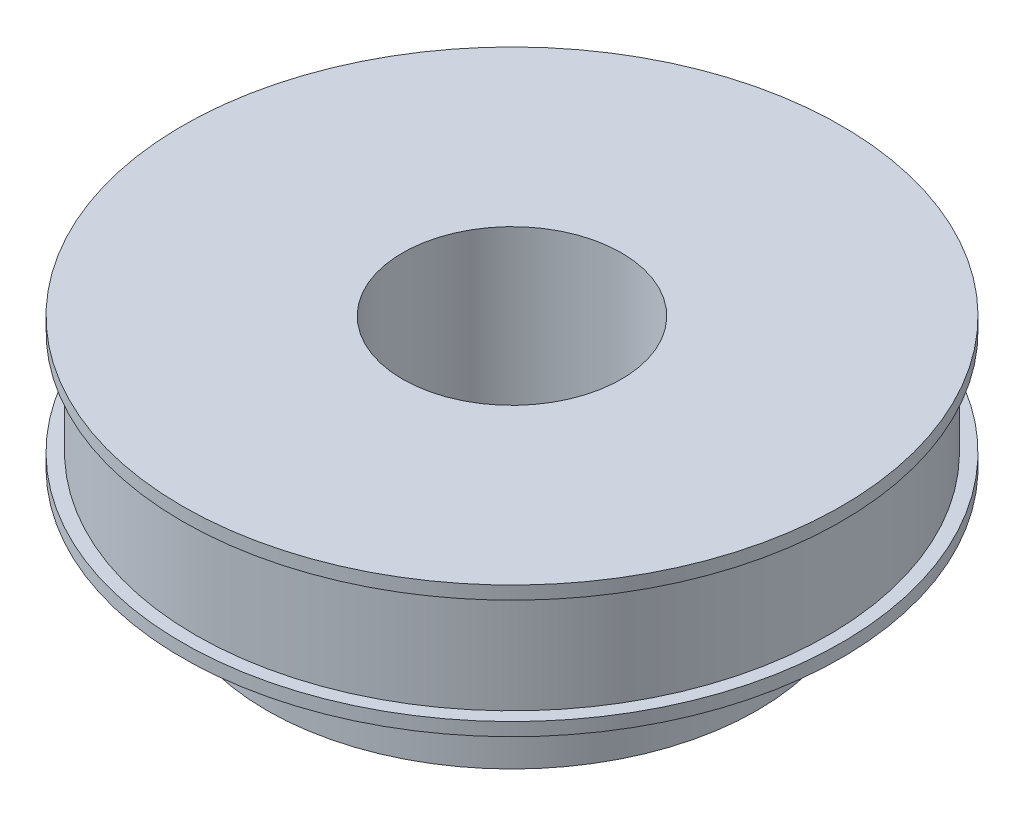
SolidWorks part; units mm, degrees
material "4032-T6"
ref_plane "Front Plane" through (0, 0, 0) normal (0, 0, 1) x (1, 0, 0)
ref_plane "Top Plane" through (0, 0, 0) normal (0, 1, 0) x (1, 0, 0)
ref_plane "Right Plane" through (0, 0, 0) normal (1, 0, 0) x (0, 0, -1)
sketch "Sketch1" plane through (0, 0, 0) normal (0, 1, 0) x (1, 0, 0)
  circle A0 centre (0, 0) radius 36.125
  dimension "D1" = 72.25
extrude "Boss-Extrude1" add sketch "Sketch1" along normal blind 12
sketch "Sketch3" plane through (0, 12, 0) normal (0, 1, 0) x (1, 0, 0)
  circle A0 centre (0, 0) radius 37.625
  dimension "D1" = 75.25
extrude "Boss-Extrude3" add sketch "Sketch3" along normal blind 1.5
sketch "Sketch4" plane through (0, 0, 0) normal (0, -1, 0) x (1, 0, 0)
  circle A0 centre (0, 0) radius 37.625
  dimension "D1" = 75.25
extrude "Boss-Extrude4" add sketch "Sketch4" along normal blind 1.5
sketch "Sketch5" plane through (0, -1.5, 0) normal (0, -1, 0) x (1, 0, 0)
  circle A0 centre (0, 0) radius 28
  dimension "D1" = 56
extrude "Boss-Extrude5" add sketch "Sketch5" along normal blind 10
sketch "Sketch6" plane through (0, 13.5, 0) normal (0, 1, 0) x (1, 0, 0)
  circle A0 centre (0, 0) radius 12.5
  dimension "D1" = 25
extrude "Cut-Extrude1" cut sketch "Sketch6" against normal up to surface (25 mm away) up to face at (0, -11.5, -28)
